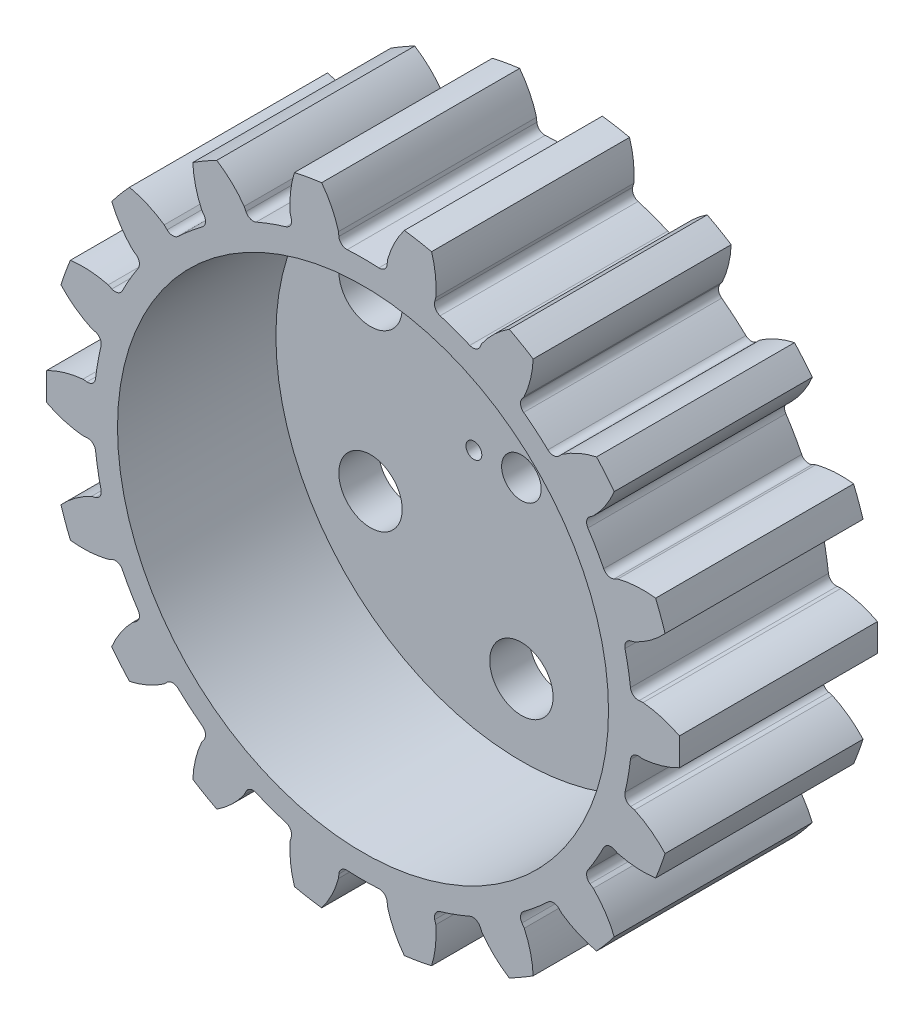
SolidWorks part; units mm, degrees
ref_plane "Plan de face" through (0, 0, 0) normal (0, 0, 1) x (1, 0, 0)
ref_plane "Plan de dessus" through (0, 0, 0) normal (0, 1, 0) x (1, 0, 0)
ref_plane "Plan de droite" through (0, 0, 0) normal (1, 0, 0) x (0, 0, -1)
sketch "Esquisse1" plane through (0, 0, 0) normal (0, 0, 1) x (1, 0, 0)
  line L0 (0, 0) -> (49.1646, 0) construction
  line L1 (0, 0) -> (33.4835, 5.904) construction
  line L2 (0, 0) -> (40.5362, 3.5465) construction
  line L3 (0, 0) -> (40.5296, 1.7696) construction
  line L4 (33.8706, -2.9633) -> (35.3649, -3.094)
  line L5 (0, 0) -> (33.4835, 5.904)
  line L6 (33.8706, 2.9633) -> (35.3649, 3.094)
  line L7 (0, 0) -> (33.4835, -5.904)
  circle A0 centre (0, 0) radius 40 construction
  circle A1 centre (0, 0) radius 35.5 construction
  circle A2 centre (0, 0) radius 34 construction
  arc A3 (33.4835, 5.904) -> (33.8706, 2.9633) centre (0, 0) cw
  arc A4 (39.9546, -1.7445) -> (39.9546, 1.7445) centre (0, 0) ccw
  arc A5 (35.3649, 3.094) -> (39.9546, 1.7445) centre (34.1869, -9.3916) cw
  arc A6 (35.3649, -3.094) -> (39.9546, -1.7445) centre (34.1869, 9.3916) ccw
  arc A7 (33.4835, -5.904) -> (33.8706, -2.9633) centre (0, 0) ccw
  dimension "D1" = 80
  dimension "D2" = 71
  dimension "D3" = 6
  dimension "D4" = 10
  dimension "D5" = 5
  dimension "D6" = 2.5
extrude "Boss.-Extru.1" add sketch "Esquisse1" along normal blind 25 contours L7 A7 L4 A6 A4 A5 L6 A3 L5
fillet "Congé1" radius 1 2 edges at (33.8706, -2.9633, 12.5) (33.8706, 2.9633, 12.5)
pattern_circular "Répétition circulaire2" count 18 over 360 about axis through (0, 0, 0) along (0, 0, 1) of "Congé1", "Boss.-Extru.1"
sketch "Esquisse10" plane through (0, 0, 25) normal (0, 0, 1) x (1, 0, 0)
  circle A0 centre (0, 0) radius 2.5
  dimension "D1" = 5
extrude "Enlèv. mat.-Extru.6" cut sketch "Esquisse10" against normal up to surface (25 mm away) up to face at (0, 0, 0)
sketch "Esquisse11" plane through (0, 0, 25) normal (0, 0, 1) x (1, 0, 0)
  circle A0 centre (0, 0) radius 31
  dimension "D1" = 62
extrude "Enlèv. mat.-Extru.7" cut sketch "Esquisse11" against normal blind 20
sketch "Esquisse12" plane through (0, 0, 0) normal (0, 0, -1) x (-1, 0, 0)
  circle A0 centre (-6, 0) radius 1
  circle A1 centre (6, 0) radius 1
  dimension "D1" = 2
  dimension "D2" = 2
  dimension "D3" = 6
  dimension "D4" = 6
extrude "Enlèv. mat.-Extru.8" cut sketch "Esquisse12" against normal up to surface (5 mm away) up to face at (31, 0, 5)
sketch "Esquisse9" plane through (0, 0, 25) normal (0, 0, 1) x (1, 0, 0)
  circle A0 centre (0, 22) radius 4
  dimension "D1" = 8
  dimension "D2" = 22
extrude "Enlèv. mat.-Extru.5" cut sketch "Esquisse9" against normal up to surface (25 mm away) up to face at (-7, 0, 0)
pattern_circular "Répétition circulaire3" count 6 over 360 about axis through (0, 0, 0) along (0, 0, 1) of "Enlèv. mat.-Extru.5"
